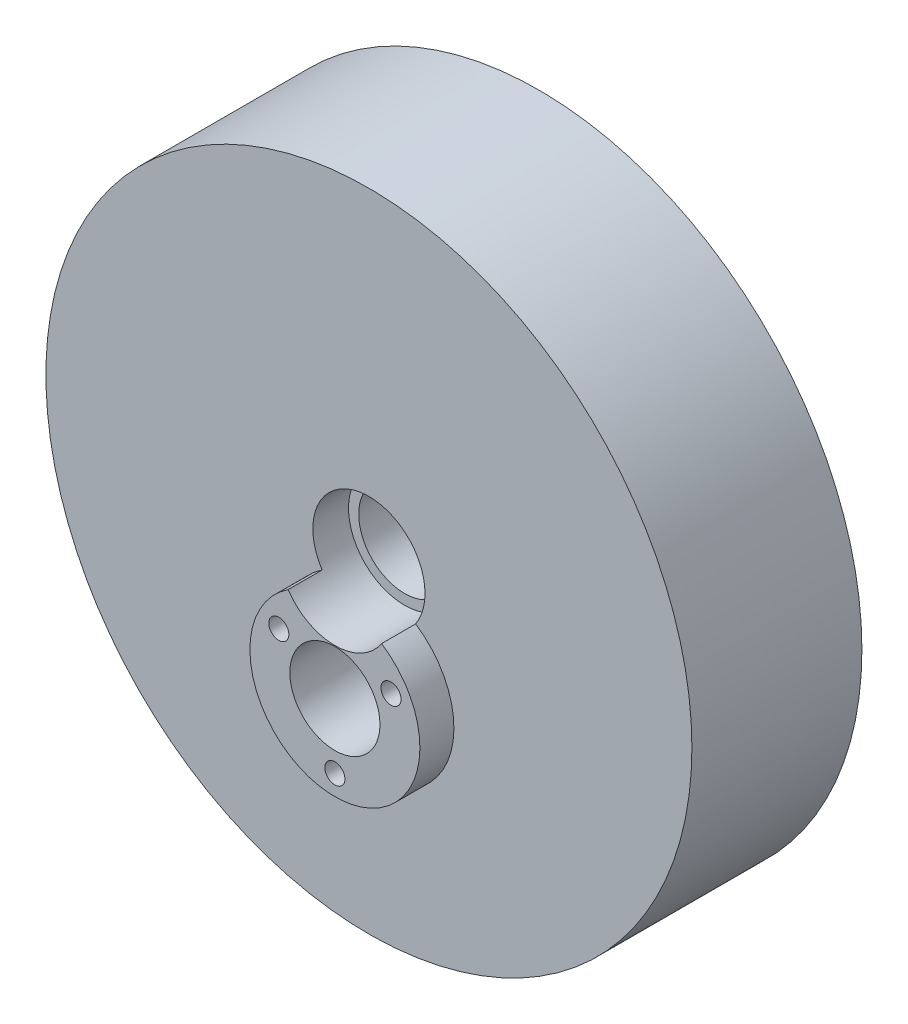
SolidWorks part; units mm, degrees
ref_plane "Front Plane" through (0, 0, 0) normal (0, 0, 1) x (1, 0, 0)
ref_plane "Top Plane" through (0, 0, 0) normal (0, 1, 0) x (1, 0, 0)
ref_plane "Right Plane" through (0, 0, 0) normal (1, 0, 0) x (0, 0, -1)
sketch "Sketch1" plane through (0, 0, 0) normal (0, 0, 1) x (1, 0, 0)
  circle A0 centre (0, 0) radius 48.26
  dimension "D1" = 96.52
extrude "Boss-Extrude1" add sketch "Sketch1" along normal blind 25.4
sketch "Sketch2" plane through (0, 0, 25.4) normal (0, 0, 1) x (1, 0, 0)
  circle A0 centre (0, 0) radius 8.382
  dimension "D1" = 16.764
extrude "Cut-Extrude1" cut sketch "Sketch2" against normal blind 5.334
sketch "Sketch12" plane through (0, 0, 0) normal (0, 0, -1) x (-1, 0, 0)
  circle A0 centre (0, -15.24) radius 6.731
  dimension "D2" = 13.462
  dimension "D1" = 15.24
extrude "Cut-Extrude5" cut sketch "Sketch12" against normal through all
sketch "Sketch15" plane through (0, 0, 25.4) normal (0, 0, 1) x (1, 0, 0)
  arc A0 (-6.985, -4.6334) -> (6.985, -4.6334) centre (0, -15.24) ccw
  circle A1 centre (0, 0) radius 8.382 construction
  circle A2 centre (0, 0) radius 8.382
  arc A3 (6.985, -4.6334) -> (-6.985, -4.6334) centre (0, 0) cw
  circle A4 centre (0, -15.24) radius 6.731
  circle A5 centre (0, -15.24) radius 6.731 construction
  circle M3 centre (0, -15.24) radius 6.731
  circle M4 centre (0, 0) radius 8.382
  dimension "D1" = 25.4
extrude "Boss-Extrude2" add sketch "Sketch15" along normal blind 5.08 contours A0 M4 M3
sketch "Sketch16" plane through (0, 0, 30.48) normal (0, 0, 1) x (1, 0, 0)
  line L0 (-8.3797, -10.402) -> (8.3797, -10.402) construction
  line L1 (8.3797, -10.402) -> (0, -24.916) construction
  line L2 (0, -24.916) -> (-8.3797, -10.402) construction
  circle A1 centre (8.3797, -10.402) radius 1.5
  circle A2 centre (0, -24.916) radius 1.5
  circle A3 centre (-8.3797, -10.402) radius 1.5
  arc A4 (-6.985, -4.6334) -> (6.985, -4.6334) centre (0, -15.24) ccw construction
  circle A5 centre (0, -15.24) radius 9.676 construction
  point P13 (0, 0)
  point P14 (0, 0)
  dimension "D1" = 3
  dimension "D2" = 1.524
extrude "Cut-Extrude9" cut sketch "Sketch16" against normal through all
ref_plane "Mid Plane" through (0, 0, 12.7) normal (0, 0, 1) x (1, 0, 0)
mirror "Mirror1" about plane through (0, 0, 12.7) normal (0, 0, 1) of "Cut-Extrude1"
sketch "Sketch14" plane through (0, 0, 25.4) normal (0, 0, 1) x (1, 0, 0)
  circle A0 centre (0, 0) radius 6.858
  circle A1 centre (0, 0) radius 48.26 construction
  circle A2 centre (0, 0) radius 8.382 construction
  dimension "D1" = 1.524
extrude "Cut-Extrude8" cut sketch "Sketch14" against normal through all
